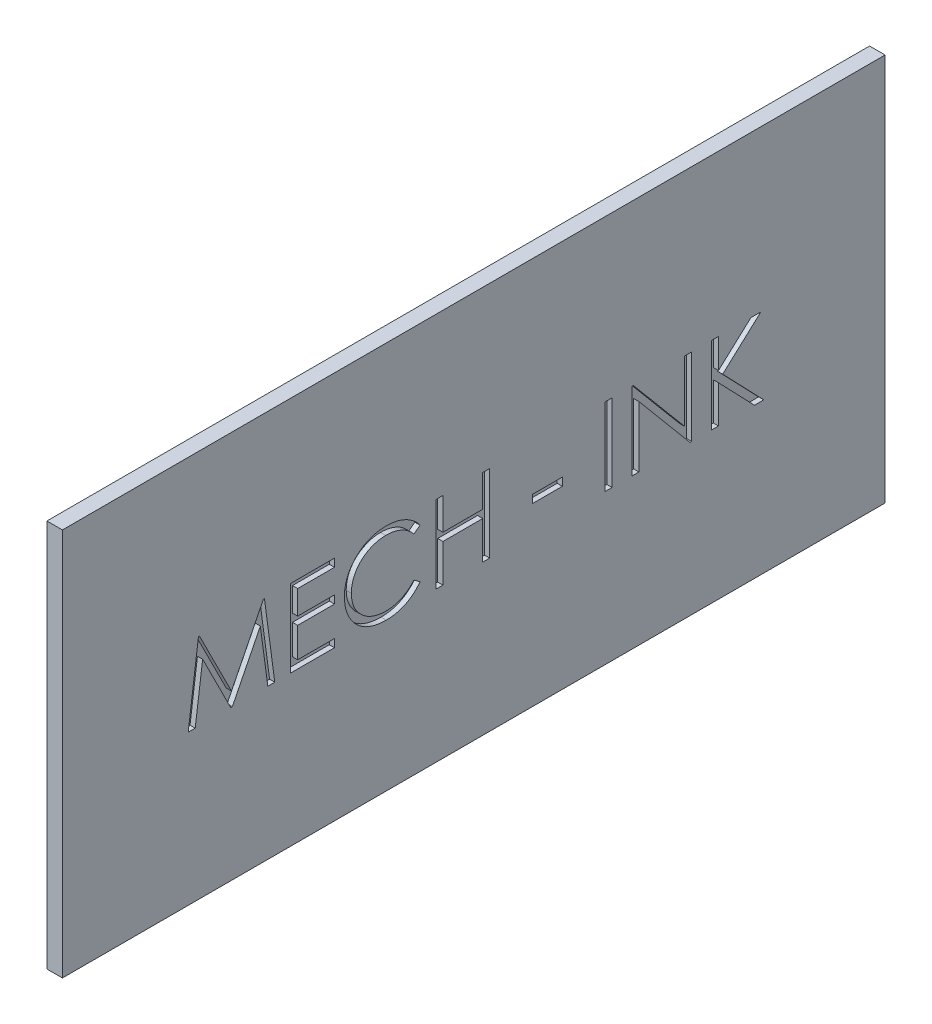
SolidWorks part; units mm, degrees
ref_plane "Front Plane" through (0, 0, 0) normal (0, 0, 1) x (1, 0, 0)
ref_plane "Top Plane" through (0, 0, 0) normal (0, 1, 0) x (1, 0, 0)
ref_plane "Right Plane" through (0, 0, 0) normal (1, 0, 0) x (0, 0, -1)
sketch "Croquis1" plane through (0, 0, 0) normal (1, 0, 0) x (0, 0, -1)
  line L1 (-79.505, 37.5) -> (79.505, 37.5)
  line L2 (-79.505, 37.5) -> (-79.505, -37.5)
  line L3 (-79.505, -37.5) -> (79.505, -37.5)
  line L4 (79.505, 37.5) -> (79.505, -37.5)
  line L5 (-79.505, 37.5) -> (79.505, -37.5) construction
  line L6 (-79.505, -37.5) -> (79.505, 37.5) construction
  point P0 (0, 0)
  dimension "D1" = 75
  dimension "D2" = 159.01
extrude "Saliente-Extruir1" add sketch "Croquis1" along normal blind 3
sketch "Croquis2" plane through (3, 0, 0) normal (1, 0, 0) x (0, 0, -1)
  line L0 (-69.4406, -8.5067) -> (69.4406, -8.5067) construction
  text T0 "MECH - INK" font "Century Gothic" height 15
  point P2 (0, -8.5067)
extrude "Cortar-Extruir1" cut sketch "Croquis2" against normal blind 1
